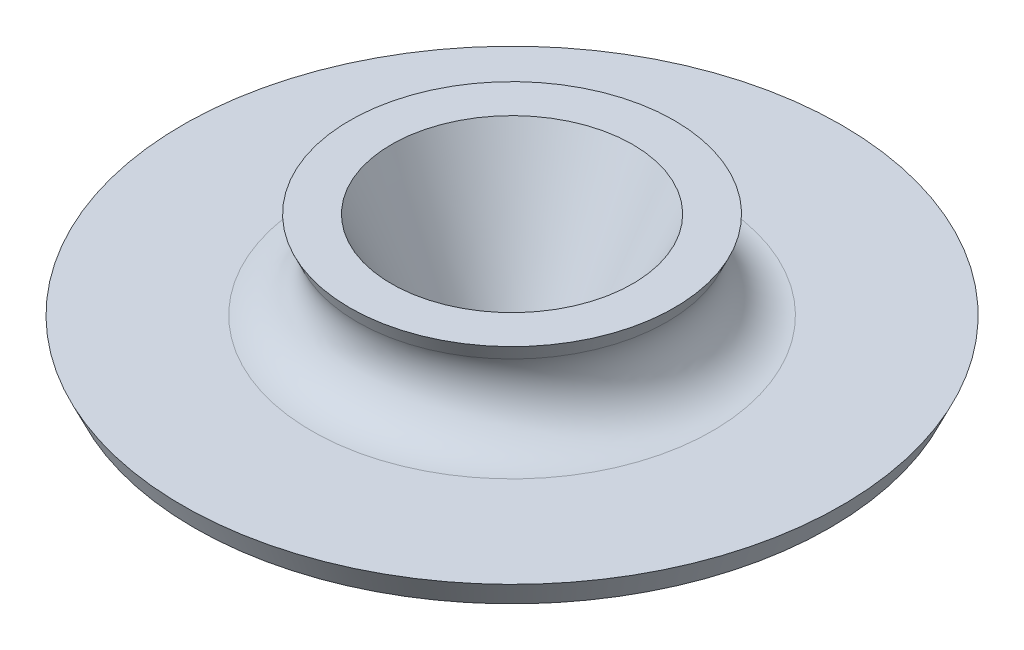
SolidWorks part; units mm, degrees
ref_plane "Front Plane" through (0, 0, 0) normal (0, 0, 1) x (1, 0, 0)
ref_plane "Top Plane" through (0, 0, 0) normal (0, 1, 0) x (1, 0, 0)
ref_plane "Right Plane" through (0, 0, 0) normal (1, 0, 0) x (0, 0, -1)
sketch "Sketch1" plane through (0, 0, 0) normal (0, 0, 1) x (1, 0, 0)
  line L0 (0, 0) -> (0, 52.0807) construction
  line L1 (-12.7, 0) -> (-19.7064, 0)
  line L2 (-19.7064, 0) -> (-24.1964, 9.6288)
  line L3 (-24.1964, 9.6288) -> (-80.248, 9.6288)
  line L4 (-80.248, 9.6288) -> (-83.2091, 15.9788)
  line L5 (-83.2091, 15.9788) -> (-30.6607, 15.9788)
  line L6 (-30.6607, 15.9788) -> (-40.976, 38.1)
  line L7 (-40.976, 38.1) -> (-30.4663, 38.1)
  line L8 (-30.4663, 38.1) -> (-12.7, 0)
  dimension "D1" = 38.1
  dimension "D2" = 6.35
  dimension "D3" = 9.6288
  dimension "D4" = 9.525
  dimension "D5" = 6.35
  dimension "D6" = 25.4
  dimension "D7" = 57.15
  dimension "D8" = 25
revolve "Revolve1" add sketch "Sketch1" angle 360 about L0
fillet "Fillet1" radius 12.7 1 edges at (0, 15.9788, -30.6607)
